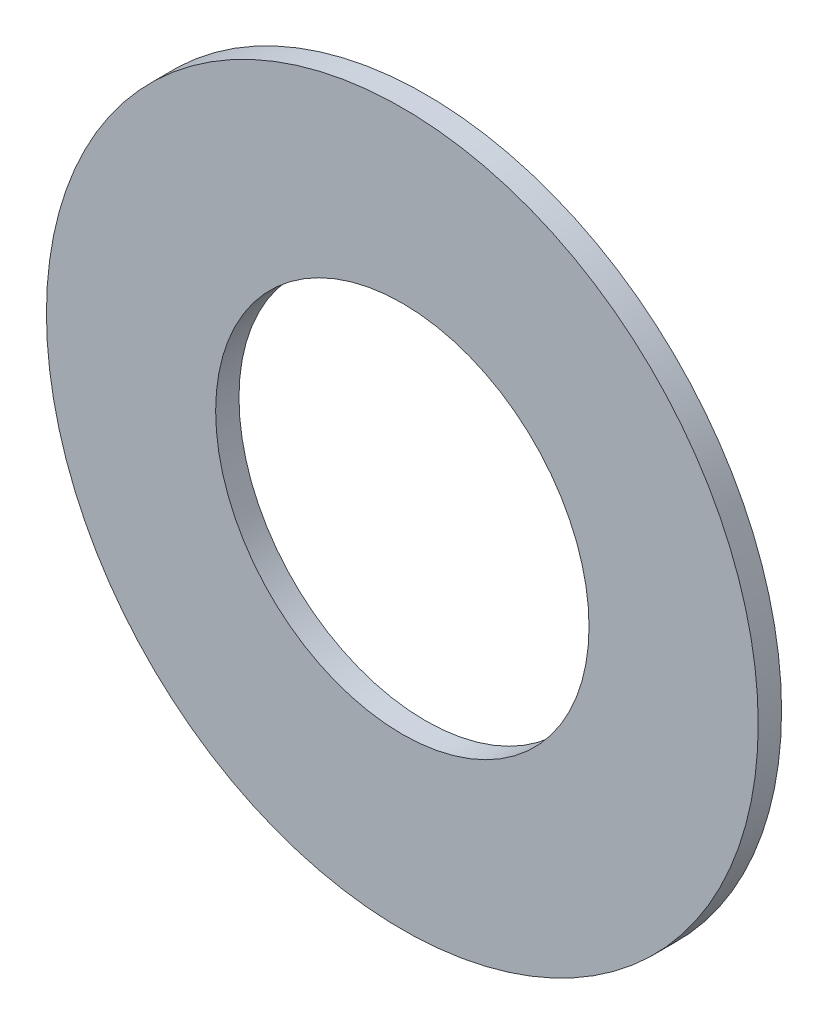
SolidWorks part; units mm, degrees
ref_plane "Face" through (0, 0, 0) normal (0, 0, 1) x (1, 0, 0)
ref_plane "Dessus" through (0, 0, 0) normal (0, 1, 0) x (1, 0, 0)
ref_plane "Droite" through (0, 0, 0) normal (1, 0, 0) x (0, 0, -1)
sketch "Esquisse1" plane through (0, 0, 0) normal (0, 0, 1) x (1, 0, 0)
  circle A0 centre (0, 0) radius 8
  circle A1 centre (0, 0) radius 15.25
  dimension "Dia int" = 16
  dimension "Dia ext" = 30.5
extrude "Base-Extrusion" add sketch "Esquisse1" along normal blind 1
